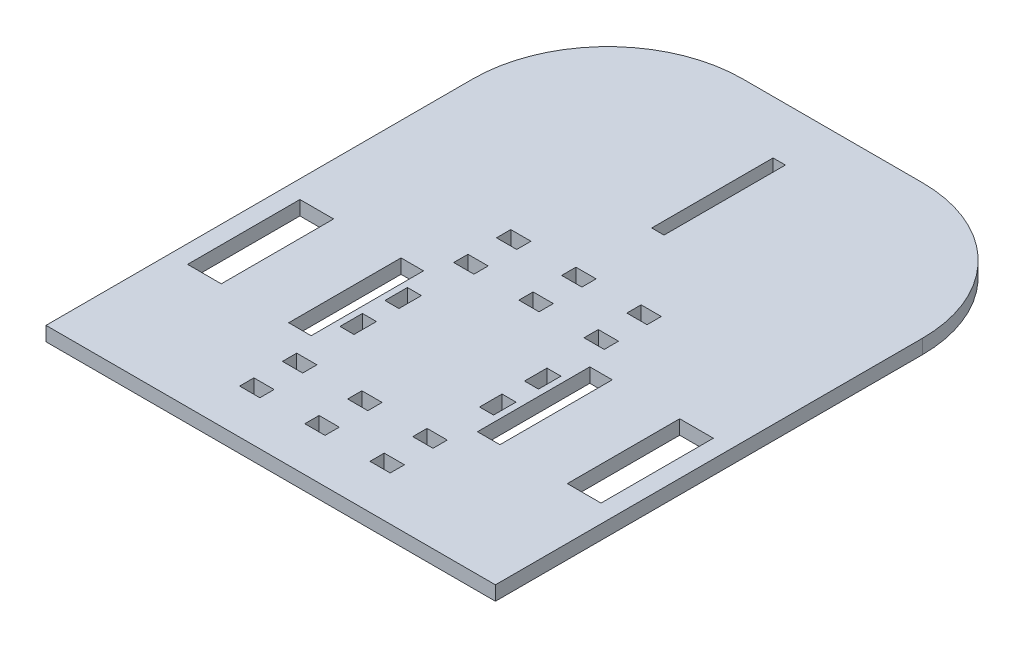
SolidWorks part; units mm, degrees
ref_plane "Front Plane" through (0, 0, 0) normal (0, 0, 1) x (1, 0, 0)
ref_plane "Top Plane" through (0, 0, 0) normal (0, 1, 0) x (1, 0, 0)
ref_plane "Right Plane" through (0, 0, 0) normal (1, 0, 0) x (0, 0, -1)
sketch "Sketch1" plane through (0, 0, 0) normal (0, 1, 0) x (1, 0, 0)
  line L0 (0, 124.3155) -> (0, -124.3155) construction
  line L1 (-100, 125) -> (100, 125)
  line L2 (-100, 125) -> (-100, -125)
  line L3 (-100, -125) -> (100, -125)
  line L4 (100, 125) -> (100, -125)
  line L5 (-100, 125) -> (100, -125) construction
  line L6 (-100, -125) -> (100, 125) construction
  line L8 (-2.7431, 101.2998) -> (2.7431, 101.2998)
  line L9 (-2.7431, 101.2998) -> (-2.7431, 47.3012)
  line L10 (-2.7431, 47.3012) -> (2.7431, 47.3012)
  line L11 (2.7431, 101.2998) -> (2.7431, 47.3012)
  line L12 (-2.7431, 101.2998) -> (2.7431, 47.3012) construction
  line L13 (-2.7431, 47.3012) -> (2.7431, 101.2998) construction
  line L14 (27.94, -50) -> (34.1673, -50)
  line L15 (27.94, -50) -> (27.94, -60)
  line L16 (27.94, -60) -> (34.1673, -60)
  line L17 (34.1673, -50) -> (34.1673, -60)
  line L18 (27.94, -50) -> (34.1673, -60) construction
  line L19 (27.94, -60) -> (34.1673, -50) construction
  line L23 (27.94, -40) -> (34.1673, -30) construction
  line L24 (27.94, -30) -> (34.1673, -30)
  line L26 (27.94, -40) -> (27.94, -30)
  line L27 (27.94, -30) -> (34.1673, -40) construction
  line L28 (-100, 125) -> (-100, -125)
  line L29 (100, 125) -> (100, -125)
  line L36 (34.1673, -40) -> (34.1673, -30)
  line L37 (27.94, -40) -> (34.1673, -40)
  line L39 (7.9781, -45) -> (50007.9781, -45) construction
  line L40 (-4.5, -79.9251) -> (4.5, -79.9251)
  line L41 (-4.5, -79.9251) -> (-4.5, -86.2749)
  line L42 (-4.5, -86.2749) -> (4.5, -86.2749)
  line L43 (4.5, -79.9251) -> (4.5, -86.2749)
  line L44 (-4.5, -79.9251) -> (4.5, -86.2749) construction
  line L45 (-4.5, -86.2749) -> (4.5, -79.9251) construction
  line L46 (-27.94, -50) -> (-34.1673, -50)
  line L47 (-27.94, -50) -> (-34.1673, -60) construction
  line L48 (-34.1673, -50) -> (-34.1673, -60)
  line L49 (-27.94, -50) -> (-27.94, -60)
  line L50 (-27.94, -60) -> (-34.1673, -50) construction
  line L51 (-27.94, -60) -> (-34.1673, -60)
  line L52 (-27.94, -40) -> (-34.1673, -40)
  line L53 (-27.94, -40) -> (-27.94, -30)
  line L54 (-27.94, -30) -> (-34.1673, -40) construction
  line L55 (-27.94, -40) -> (-34.1673, -30) construction
  line L56 (-34.1673, -40) -> (-34.1673, -30)
  line L57 (-27.94, -30) -> (-34.1673, -30)
  line L65 (24.5, -79.925) -> (33.5, -79.925)
  line L66 (24.5, -79.925) -> (24.5, -86.275)
  line L67 (24.5, -86.275) -> (33.5, -86.275)
  line L68 (33.5, -79.925) -> (33.5, -86.275)
  line L69 (24.5, -79.925) -> (33.5, -86.275) construction
  line L70 (24.5, -86.275) -> (33.5, -79.925) construction
  line L75 (-92, -20) -> (-77, -20)
  line L76 (-92, -20) -> (-92, -70)
  line L77 (-92, -70) -> (-77, -70)
  line L82 (-33.5, -79.925) -> (-33.5, -86.275)
  line L83 (-24.5, -86.275) -> (-33.5, -86.275)
  line L84 (-24.5, -86.275) -> (-33.5, -79.925) construction
  line L85 (-24.5, -79.925) -> (-33.5, -86.275) construction
  line L86 (-24.5, -79.925) -> (-24.5, -86.275)
  line L87 (-24.5, -79.925) -> (-33.5, -79.925)
  line L106 (-992.0219, -83.1) -> (49007.9781, -83.1) construction
  line L107 (31.0537, -1055.0562) -> (31.0537, 48944.9438) construction
  line L108 (-1000, -92.6249) -> (49000, -92.6249) construction
  line L113 (24.5, -98.9748) -> (33.5, -98.9748)
  line L114 (33.5, -105.3249) -> (33.5, -98.9748)
  line L115 (24.5, -105.3249) -> (33.5, -105.3249)
  line L116 (24.5, -105.3249) -> (24.5, -98.9748)
  line L117 (-4.5, -98.9749) -> (4.5, -98.9749)
  line L118 (4.5, -105.3248) -> (4.5, -98.9749)
  line L119 (-4.5, -105.3248) -> (4.5, -105.3248)
  line L120 (-4.5, -105.3248) -> (-4.5, -98.9749)
  line L121 (-24.5, -105.3249) -> (-33.5, -105.3249)
  line L122 (-24.5, -105.3249) -> (-24.5, -98.9748)
  line L123 (-24.5, -98.9748) -> (-33.5, -98.9748)
  line L124 (-33.5, -105.3249) -> (-33.5, -98.9748)
  line L129 (-4.5, -3.7251) -> (4.5, -3.7251)
  line L130 (4.5, -10.0749) -> (4.5, -3.7251)
  line L131 (-4.5, -10.0749) -> (4.5, -10.0749)
  line L132 (-4.5, -10.0749) -> (-4.5, -3.7251)
  line L133 (24.5, -3.725) -> (33.5, -3.725)
  line L134 (33.5, -10.075) -> (33.5, -3.725)
  line L135 (24.5, -10.075) -> (33.5, -10.075)
  line L136 (24.5, -10.075) -> (24.5, -3.725)
  line L145 (24.5, 15.3249) -> (24.5, 8.9748)
  line L146 (24.5, 15.3249) -> (33.5, 15.3249)
  line L147 (33.5, 15.3249) -> (33.5, 8.9748)
  line L148 (24.5, 8.9748) -> (33.5, 8.9748)
  line L149 (-4.5, 15.3248) -> (-4.5, 8.9749)
  line L150 (-4.5, 15.3248) -> (4.5, 15.3248)
  line L151 (4.5, 15.3248) -> (4.5, 8.9749)
  line L152 (-4.5, 8.9749) -> (4.5, 8.9749)
  line L153 (-24.5, 15.3249) -> (-24.5, 8.9748)
  line L154 (-24.5, 8.9748) -> (-33.5, 8.9748)
  line L155 (-33.5, 15.3249) -> (-33.5, 8.9748)
  line L156 (-24.5, 15.3249) -> (-33.5, 15.3249)
  line L157 (-24.5, -10.075) -> (-33.5, -10.075)
  line L158 (-24.5, -10.075) -> (-24.5, -3.725)
  line L159 (-24.5, -3.725) -> (-33.5, -3.725)
  line L160 (-33.5, -10.075) -> (-33.5, -3.725)
  line L161 (-77, -20) -> (-77, -70)
  line L162 (-92, -20) -> (-77, -70) construction
  line L163 (-92, -70) -> (-77, -20) construction
  line L168 (-47, -20) -> (-37, -20)
  line L169 (-47, -20) -> (-47, -70)
  line L170 (-47, -70) -> (-37, -70)
  line L171 (-37, -20) -> (-37, -70)
  line L172 (-47, -20) -> (-37, -70) construction
  line L173 (-47, -70) -> (-37, -20) construction
  line L174 (92, -70) -> (77, -70)
  line L175 (77, -20) -> (77, -70)
  line L176 (92, -20) -> (77, -20)
  line L177 (92, -20) -> (92, -70)
  line L178 (47, -70) -> (37, -70)
  line L179 (37, -20) -> (37, -70)
  line L180 (47, -20) -> (37, -20)
  line L181 (47, -20) -> (47, -70)
  point P0 (0, 0)
  point P6 (0, 74.3005)
  point P9 (0, 0)
  point P14 (31.0537, -55)
  point P22 (31.0537, -35)
  point P27 (-31.0537, -55)
  point P31 (0, -83.1)
  point P36 (-31.0537, -35)
  point P41 (0.0096, -59.601)
  point P46 (29, -83.1)
  point P52 (-84.5, -45)
  point P62 (-42, -45)
  point P67 (-29, -83.1)
  dimension "D1" = 10
  dimension "D4" = 9
  dimension "D2" = 5
  dimension "D5" = 9
  dimension "D6" = 20
  dimension "D9" = 0
  dimension "D11" = 38.1
  dimension "D12" = 80
  dimension "D3" = 6.35
  dimension "D7" = 6.3501
  dimension "D8" = 27.94
  dimension "D10" = 8
  dimension "D13" = 200
  dimension "D14" = 250
  dimension "D15" = 50
  dimension "D16" = 15
  dimension "D17" = 50
  dimension "D18" = 10
  dimension "D19" = 30
extrude "Boss-Extrude1" add sketch "Sketch1" along normal blind 6.35
fillet "Fillet1" radius 60 2 edges at (100, 3.175, -125) (-100, 3.175, -125)
equation "\"toothBaseWidth\"=0.01"
equation "\"toothEndWidth\"=0.0075"
equation "\"toothLength\"=0.0075"
equation "\"holeWidth\" = 0.009"
equation "\"motorHolderToothSeparation\" = 0.01"
equation "\"magnetHolderToothSeparation\" = 0.02"
equation "\"D2@Sketch1\"= \"motorHolderToothSeparation\"/2"
equation "\"D5@Sketch1\"= \"holeWidth\""
equation "\"D4@Sketch1\"= \"holeWidth\""
equation "\"D6@Sketch1\"= \"magnetHolderToothSeparation\""
equation "\"magnetWidth\" = 0.0127"
equation "\"quarterInch\" = 0.00635"
equation "\"D3@Sketch1\"= \"quarterInch\""
equation "\"coilThickness\" = 0.0254"
equation "\"coilOuterDiameter\" = 0.0508"
equation "\"legoThickness\" = 0.008"
equation "\"legoWidth\" = 0.016"
equation "\"D10@Sketch1\"= \"legoThickness\""
